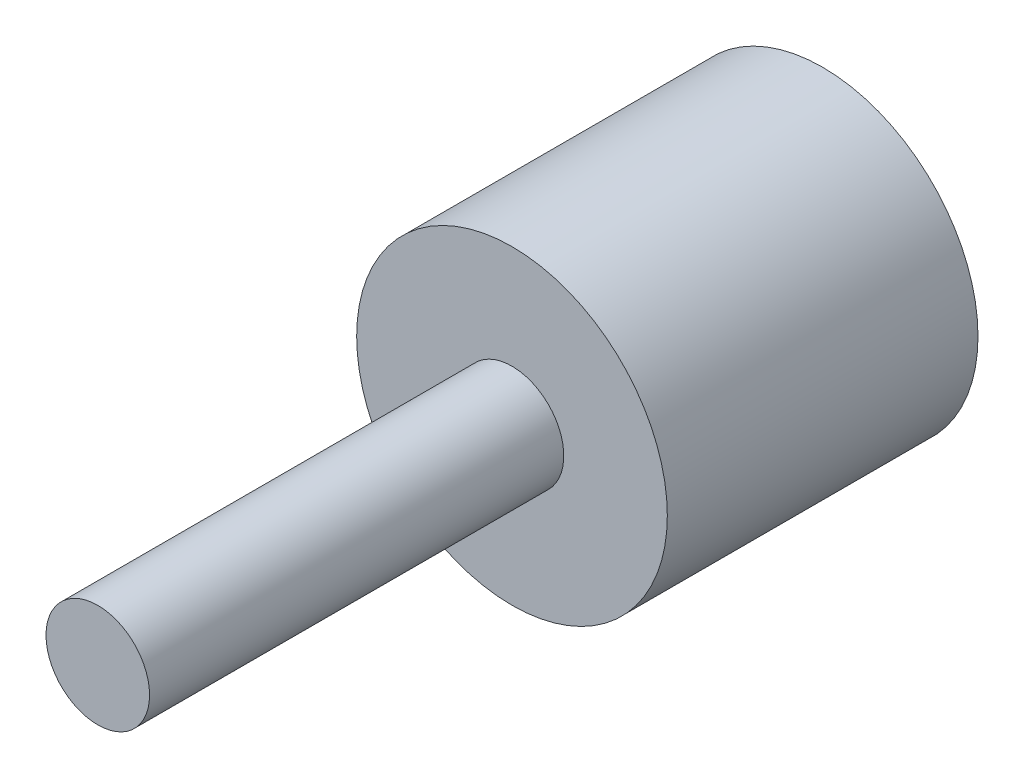
SolidWorks part; units mm, degrees
ref_plane "Front Plane" through (0, 0, 0) normal (0, 0, 1) x (1, 0, 0)
ref_plane "Top Plane" through (0, 0, 0) normal (0, 1, 0) x (1, 0, 0)
ref_plane "Right Plane" through (0, 0, 0) normal (1, 0, 0) x (0, 0, -1)
sketch "Sketch1" plane through (0, 0, 0) normal (0, 0, 1) x (1, 0, 0)
  circle A0 centre (0, 0) radius 7.5
  dimension "D1" = 15
extrude "Boss-Extrude1" add sketch "Sketch1" along normal blind 15
sketch "Sketch2" plane through (0, 0, 15) normal (0, 0, 1) x (1, 0, 0)
  circle A0 centre (0, 0) radius 2.5
  dimension "D1" = 5
extrude "Boss-Extrude2" add sketch "Sketch2" along normal blind 20
sketch "Sketch3" plane through (0, 0, 0) normal (0, 0, -1) x (-1, 0, 0)
  circle A0 centre (0, 0) radius 2.5
  dimension "D1" = 5
extrude "Cut-Extrude1" cut sketch "Sketch3" against normal blind 15
